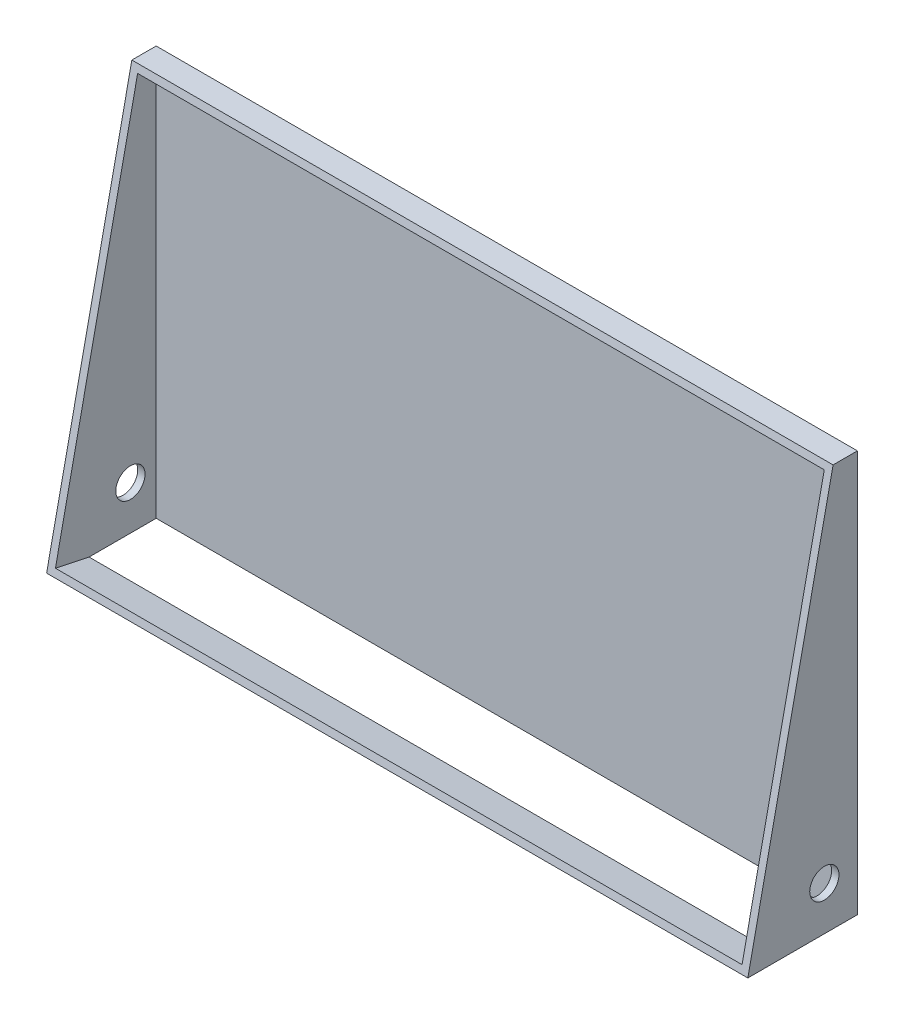
SolidWorks part; units mm, degrees
ref_plane "Alzado" through (0, 0, 0) normal (0, 0, 1) x (1, 0, 0)
ref_plane "Planta" through (0, 0, 0) normal (0, 1, 0) x (1, 0, 0)
ref_plane "Vista lateral" through (0, 0, 0) normal (1, 0, 0) x (0, 0, -1)
sketch "Croquis1" plane through (0, 0, 0) normal (0, 0, 1) x (1, 0, 0)
  line L1 (-48, 27.5) -> (48, 27.5)
  line L2 (-48, 27.5) -> (-48, -27.5)
  line L3 (-48, -27.5) -> (48, -27.5)
  line L4 (48, 27.5) -> (48, -27.5)
  line L5 (-48, 27.5) -> (48, -27.5) construction
  line L6 (-48, -27.5) -> (48, 27.5) construction
  point P0 (0, 0)
  dimension "D1" = 96
  dimension "D2" = 55
extrude "Saliente-Extruir2" add sketch "Croquis1" along normal blind 15 contours L2 L1 L4 L3
sketch "Croquis2" plane through (-48, 0, 0) normal (-1, 0, 0) x (0, 0, 1)
  line L0 (-21.6694, 0) -> (36.7786, 0) construction
  line L1 (7.5546, 0) -> (7.5546, -32.8595) construction
  line L4 (15, 27.5) -> (0, 27.5) construction
  line L5 (3.3298, 27.5) -> (15, 27.5)
  line L7 (3.3298, 27.5) -> (15, -27.5)
  line L8 (15, -27.5) -> (15, 27.5)
extrude "Cortar-Extruir1" cut sketch "Croquis2" against normal blind 96
sketch "Croquis4" plane through (0, 1.8609, 8.7701) normal (0, 0.2076, 0.9782) x (1, 0, 0)
  line L0 (-47, 25.2099) -> (-47, -29.0145)
  line L1 (-47, -29.0145) -> (47, -29.0145)
  line L2 (47, -29.0145) -> (47, 25.2099)
  line L3 (47, 25.2099) -> (-47, 25.2099)
  line L4 (-48, 26.2099) -> (-48, -30.0145)
  line L5 (-48, -30.0145) -> (48, -30.0145)
  line L6 (48, -30.0145) -> (48, 26.2099)
  line L7 (48, 26.2099) -> (-48, 26.2099)
  line L8 (-48, 26.2099) -> (-48, -30.0145)
  line L9 (-48, -30.0145) -> (48, -30.0145)
  line L10 (48, -30.0145) -> (48, 26.2099)
  line L11 (48, 26.2099) -> (-48, 26.2099)
  dimension "D1" = 0
  dimension "D2" = 1
extrude "Cortar-Extruir6" cut sketch "Croquis4" against normal offset from surface (14.0995 mm away) 1 contours L2 L3 L0 L1
sketch "Croquis5" plane through (-48, 0, 0) normal (-1, 0, 0) x (0, 0, 1)
  line L0 (-8.6582, 0) -> (21.5762, 0) construction
  line L1 (6.459, 31.3206) -> (6.459, -34.9415) construction
  line L2 (15, -27.5) -> (0, -27.5) construction
  line L3 (3.3298, 27.5) -> (15, -27.5) construction
  line L4 (0, 27.5) -> (0, -27.5) construction
  circle A0 centre (4.5265, -21.5) radius 2
  dimension "D1" = 6
  dimension "D3" = 4.5265
  dimension "D2" = 9
extrude "Cortar-Extruir7" cut sketch "Croquis5" against normal through all
